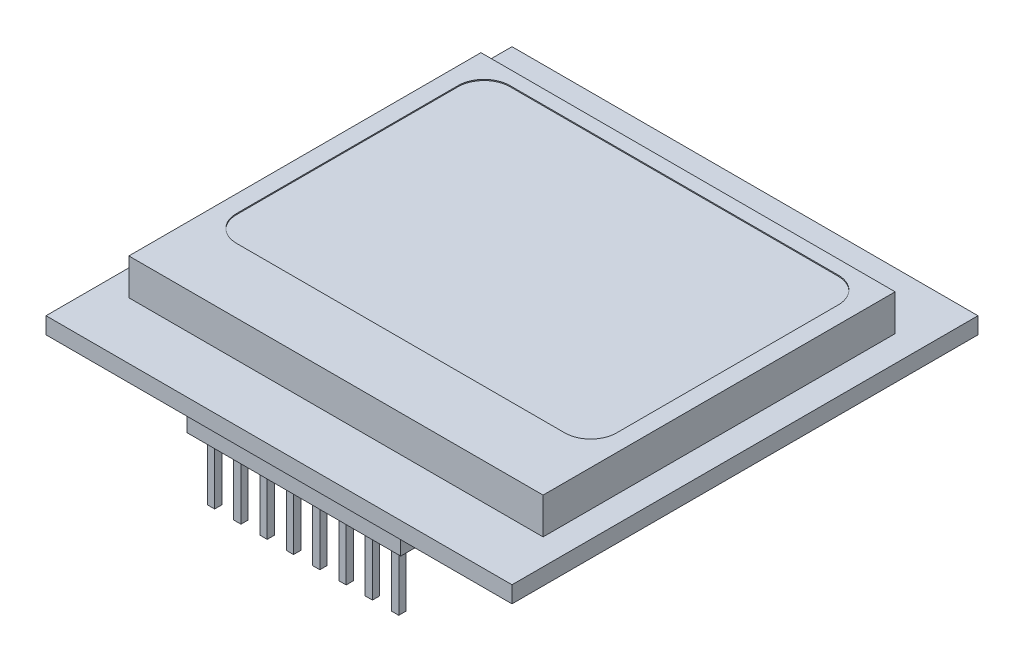
SolidWorks part; units mm, degrees
ref_plane "Front Plane" through (0, 0, 0) normal (0, 0, 1) x (1, 0, 0)
ref_plane "Top Plane" through (0, 0, 0) normal (0, 1, 0) x (1, 0, 0)
ref_plane "Right Plane" through (0, 0, 0) normal (1, 0, 0) x (0, 0, -1)
sketch "Sketch1" plane through (0, 0, 0) normal (0, 1, 0) x (1, 0, 0)
  line L1 (-22.5, 22.5) -> (22.5, 22.5)
  line L2 (-22.5, 22.5) -> (-22.5, -22.5)
  line L3 (-22.5, -22.5) -> (22.5, -22.5)
  line L4 (22.5, 22.5) -> (22.5, -22.5)
  line L5 (-22.5, 22.5) -> (22.5, -22.5) construction
  line L6 (-22.5, -22.5) -> (22.5, 22.5) construction
  point P0 (0, 0)
  dimension "D1" = 45
  dimension "D2" = 45
extrude "Boss-Extrude1" add sketch "Sketch1" along normal blind 1.6
sketch "Sketch2" plane through (0, 1.6, 0) normal (0, 1, 0) x (1, 0, 0)
  line L1 (-20, 17) -> (20, 17)
  line L2 (-20, 17) -> (-20, -17)
  line L3 (-20, -17) -> (20, -17)
  line L4 (20, 17) -> (20, -17)
  line L5 (-20, 17) -> (20, -17) construction
  line L6 (-20, -17) -> (20, 17) construction
  point P0 (0, 0)
  dimension "D1" = 40
  dimension "D2" = 34
extrude "Boss-Extrude2" add sketch "Sketch2" along normal blind 3.5
sketch "Sketch4" plane through (0, 0, 0) normal (0, -1, 0) x (1, 0, 0)
  line L0 (0, 22.5) -> (0, -22.5) construction
  line L1 (-22.5, 22.5) -> (22.5, 22.5) construction
  line L2 (22.5, -22.5) -> (-22.5, -22.5) construction
  line L3 (0, 21.075) -> (0, 18.575) construction
  line L4 (-10.33, 21.075) -> (10.33, 21.075)
  line L5 (-10.33, 21.075) -> (-10.33, 18.575)
  line L6 (-10.33, 18.575) -> (10.33, 18.575)
  line L7 (10.33, 21.075) -> (10.33, 18.575)
  line L8 (-10.33, 19.825) -> (10.33, 19.825) construction
  line L9 (-22.5, 0) -> (22.5, 0) construction
  line L10 (-22.5, -22.5) -> (-22.5, 22.5) construction
  line L11 (22.5, 22.5) -> (22.5, -22.5) construction
  dimension "D1" = 20.66
  dimension "D2" = 2.5
  dimension "D3" = 19.825
extrude "Boss-Extrude3" add sketch "Sketch4" along normal blind 2.8
sketch "Sketch5" plane through (0, -2.8, 0) normal (0, -1, 0) x (1, 0, 0)
  line L0 (-10.33, 19.825) -> (10.33, 19.825) construction
  line L1 (0, 21.075) -> (0, 18.575) construction
  line L2 (1.62, 20.175) -> (1.62, 19.475)
  line L3 (-1.62, 20.175) -> (-0.92, 20.175)
  line L4 (-10.33, 21.075) -> (-10.33, 18.575)
  line L5 (-10.33, 18.575) -> (10.33, 18.575)
  line L6 (10.33, 18.575) -> (10.33, 21.075)
  line L7 (10.33, 21.075) -> (-10.33, 21.075)
  line L8 (-10.33, 21.075) -> (-10.33, 18.575)
  line L9 (-10.33, 18.575) -> (10.33, 18.575)
  line L10 (10.33, 18.575) -> (10.33, 21.075)
  line L11 (10.33, 21.075) -> (-10.33, 21.075)
  line L12 (-1.62, 20.175) -> (-1.62, 19.475)
  line L13 (-1.62, 19.475) -> (-0.92, 19.475)
  line L14 (-0.92, 20.175) -> (-0.92, 19.475)
  line L15 (-1.62, 20.175) -> (-0.92, 19.475) construction
  line L16 (-1.62, 19.475) -> (-0.92, 20.175) construction
  line L17 (0.92, 19.475) -> (1.62, 19.475)
  line L18 (0.92, 20.175) -> (0.92, 19.475)
  line L19 (0.92, 20.175) -> (1.62, 20.175)
  line L20 (4.16, 20.175) -> (4.16, 19.475)
  line L21 (3.46, 19.475) -> (4.16, 19.475)
  line L22 (3.46, 20.175) -> (3.46, 19.475)
  line L23 (3.46, 20.175) -> (4.16, 20.175)
  line L24 (6.7, 20.175) -> (6.7, 19.475)
  line L25 (6, 19.475) -> (6.7, 19.475)
  line L26 (6, 20.175) -> (6, 19.475)
  line L27 (6, 20.175) -> (6.7, 20.175)
  line L28 (9.24, 20.175) -> (9.24, 19.475)
  line L29 (8.54, 19.475) -> (9.24, 19.475)
  line L30 (8.54, 20.175) -> (8.54, 19.475)
  line L31 (8.54, 20.175) -> (9.24, 20.175)
  line L32 (-3.46, 20.175) -> (-3.46, 19.475)
  line L33 (-4.16, 19.475) -> (-3.46, 19.475)
  line L34 (-4.16, 20.175) -> (-4.16, 19.475)
  line L35 (-4.16, 20.175) -> (-3.46, 20.175)
  line L36 (-6, 20.175) -> (-6, 19.475)
  line L37 (-6.7, 19.475) -> (-6, 19.475)
  line L38 (-6.7, 20.175) -> (-6.7, 19.475)
  line L39 (-6.7, 20.175) -> (-6, 20.175)
  line L40 (-8.54, 20.175) -> (-8.54, 19.475)
  line L41 (-9.24, 19.475) -> (-8.54, 19.475)
  line L42 (-9.24, 20.175) -> (-9.24, 19.475)
  line L43 (-9.24, 20.175) -> (-8.54, 20.175)
  point P8 (-1.27, 19.825)
  dimension "D2" = 0.7
  dimension "D3" = 0.7
  dimension "D4" = 2.54
  dimension "D1" = 0
  dimension "D5" = 5
  dimension "D6" = 4
extrude "Boss-Extrude4" add sketch "Sketch5" along normal blind 5.95 contours L43 L42 L41 L40 | L39 L38 L37 L36 | L35 L34 L33 L32 | L14 L3 L12 L13 | L19 L18 L17 L2 | L23 L22 L21 L20 | L27 L26 L25 L24 | L31 L30 L29 L28
sketch "Sketch6" plane through (0, 5.1, 0) normal (0, 1, 0) x (1, 0, 0)
  line L0 (0, 17) -> (0, -17) construction
  line L1 (20, 17) -> (-20, 17) construction
  line L2 (-20, -17) -> (20, -17) construction
  line L4 (-15.85, 15.65) -> (15.85, 15.65)
  line L5 (-18.35, 13.15) -> (-18.35, -8.25)
  line L6 (-15.85, -10.75) -> (15.85, -10.75)
  line L7 (18.35, 13.15) -> (18.35, -8.25)
  line L8 (-18.35, 15.65) -> (18.35, -10.75) construction
  line L9 (-18.35, -10.75) -> (18.35, 15.65) construction
  arc A0 (-18.35, -8.25) -> (-15.85, -10.75) centre (-15.85, -8.25) ccw
  arc A1 (15.85, -10.75) -> (18.35, -8.25) centre (15.85, -8.25) ccw
  arc A2 (15.85, 15.65) -> (18.35, 13.15) centre (15.85, 13.15) cw
  arc A3 (-15.85, 15.65) -> (-18.35, 13.15) centre (-15.85, 13.15) ccw
  point P6 (0, 2.45)
  dimension "D4" = 2.5
  dimension "D1" = 36.7
  dimension "D2" = 26.4
  dimension "D3" = 1.35
extrude "Cut-Extrude1" cut sketch "Sketch6" against normal blind 0.1
mirror "Mirror1" about plane through (0, 0, 0) normal (0, 0, 1) of "Boss-Extrude4", "Boss-Extrude3"
equation "\"D3@Sketch4\"=39.65/2"
